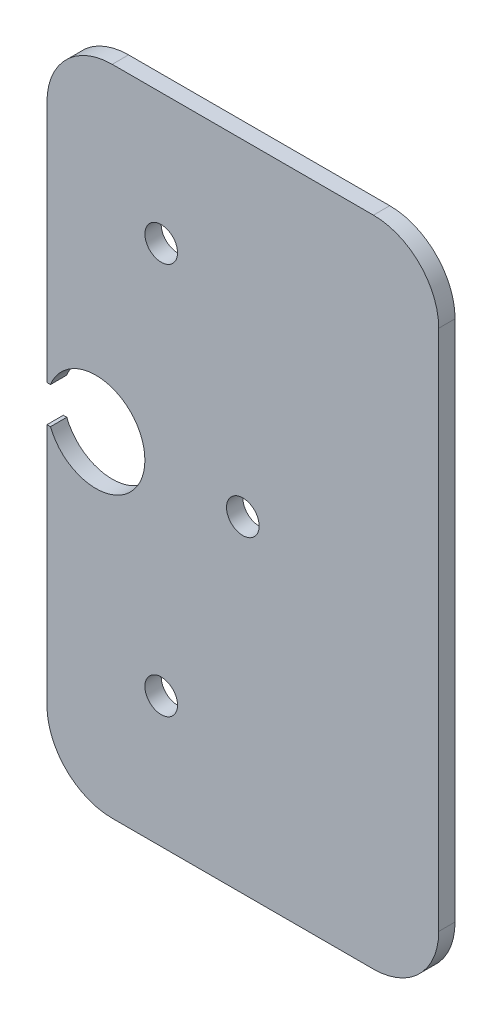
SolidWorks part; units mm, degrees
ref_plane "Front Plane" through (0, 0, 0) normal (0, 0, 1) x (1, 0, 0)
ref_plane "Top Plane" through (0, 0, 0) normal (0, 1, 0) x (1, 0, 0)
ref_plane "Right Plane" through (0, 0, 0) normal (1, 0, 0) x (0, 0, -1)
sketch "Sketch1" plane through (0, 0, 0) normal (0, 0, 1) x (1, 0, 0)
  line L0 (-459.74, 1028.0012) -> (-459.0589, 1028.0012)
  line L1 (-459.74, 1024.4555) -> (-440.69, 1024.4555) construction
  line L2 (-459.74, 1020.9099) -> (-459.0589, 1020.9099)
  line L3 (-459.74, 1028.0012) -> (-459.74, 1075.2555)
  line L4 (-447.04, 960.9555) -> (-396.24, 960.9555)
  line L5 (-459.74, 973.6555) -> (-459.74, 1020.9099)
  line L6 (-447.04, 1087.9555) -> (-396.24, 1087.9555)
  line L7 (-383.54, 973.6555) -> (-383.54, 1075.2555)
  circle A0 centre (-437.515, 1062.5555) radius 3.175 construction
  circle A1 centre (-437.515, 986.3555) radius 3.175 construction
  circle A2 centre (-421.64, 1024.4555) radius 3.175 construction
  circle A3 centre (-437.515, 1062.5555) radius 3.175
  circle A4 centre (-437.515, 986.3555) radius 3.175
  circle A5 centre (-421.64, 1024.4555) radius 3.175
  arc A6 (-396.24, 960.9555) -> (-383.54, 973.6555) centre (-396.24, 973.6555) ccw
  arc A7 (-447.04, 960.9555) -> (-459.74, 973.6555) centre (-447.04, 973.6555) cw
  arc A8 (-396.24, 1087.9555) -> (-383.54, 1075.2555) centre (-396.24, 1075.2555) cw
  arc A9 (-459.74, 1075.2555) -> (-447.04, 1087.9555) centre (-447.04, 1075.2555) cw
  ellipse E0 centre (-450.215, 1024.4555) end of major axis (-450.215, 1034.0035) minor radius 9.525 construction
  ellipse E1 centre (-450.215, 1024.4555) end of major axis (-450.215, 1034.0035) minor radius 9.525 (-459.0589, 1020.9099) -> (-459.0589, 1028.0012) ccw
  point P31 (-459.74, 960.9555)
  point P36 (-459.74, 1087.9555)
  dimension "D3" = 12.7
  dimension "D1" = 127
  dimension "D2" = 76.2
extrude "Boss-Extrude2" add sketch "Sketch1" along normal blind 3.175 contours E1 L2 L5 A7 L4 A6 L7 A8 L6 A9 L3 L0 A5 A4 A3
